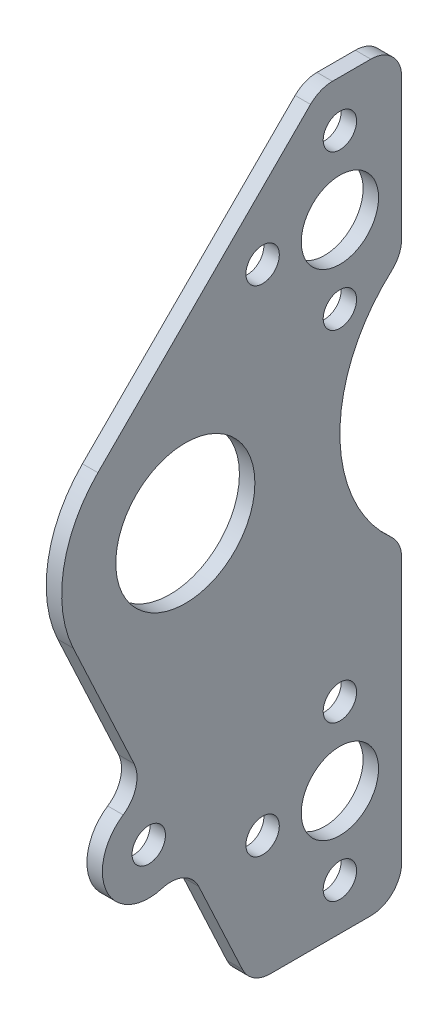
SolidWorks part; units mm, degrees
ref_plane "Front Plane" through (0, 0, 0) normal (0, 0, 1) x (1, 0, 0)
ref_plane "Top Plane" through (0, 0, 0) normal (0, 1, 0) x (1, 0, 0)
ref_plane "Right Plane" through (0, 0, 0) normal (1, 0, 0) x (0, 0, -1)
sketch "Sketch1" plane through (0, 0, 0) normal (1, 0, 0) x (0, 0, -1)
  line L0 (0, 55) -> (0, -55) construction
  line L1 (-19.05, 0) -> (-26.5619, -53.4497) construction
  line L2 (12.7, 38.1) -> (12.7, 53.975) construction
  line L3 (12.7, 38.1) -> (-3.175, 38.1) construction
  line L4 (12.7, -63.5) -> (-3.175, -63.5) construction
  line L5 (25.4, 57.15) -> (25.4, 28.3981)
  line L6 (19.05, -88.9) -> (-1.5757, -88.9)
  line L8 (11.1592, 63.5) -> (19.05, 63.5)
  line L9 (55, 0) -> (-55, 0) construction
  line L10 (-37.0105, 17.9605) -> (6.6691, 61.6401)
  line L11 (-42.0702, -10.7345) -> (-29.5744, -37.5319)
  line L12 (-16.3045, -65.9893) -> (-7.3307, -85.2336)
  line L13 (25.4, -28.3981) -> (25.4, -82.55)
  circle A0 centre (-19.05, 0) radius 14.2875
  circle A1 centre (12.7, 38.1) radius 7.9375
  circle A2 centre (12.7, -63.5) radius 7.9375
  circle A3 centre (-26.5619, -53.4497) radius 3.429
  circle A4 centre (12.7, 38.1) radius 15.875 construction
  circle A6 centre (12.7, 53.975) radius 3.429
  circle A8 centre (12.7, -63.5) radius 15.875 construction
  circle A9 centre (-3.175, -63.5) radius 3.429
  circle A10 centre (12.7, -47.625) radius 3.429
  circle A12 centre (12.7, -79.375) radius 3.429
  arc A14 (25.4, -82.55) -> (19.05, -88.9) centre (19.05, -82.55) cw
  arc A15 (25.4, 57.15) -> (19.05, 63.5) centre (19.05, 57.15) ccw
  circle A17 centre (-3.175, 38.1) radius 3.429
  circle A18 centre (12.7, 22.225) radius 3.429
  circle A19 centre (28.575, -63.5) radius 3.429 [skipped]
  arc A20 (-37.0105, 17.9605) -> (-42.0702, -10.7345) centre (-19.05, 0) ccw
  arc A21 (-31.8224, -45.5092) -> (-23.8605, -62.5836) centre (-26.5619, -53.4497) ccw
  arc A22 (-16.3045, -65.9893) -> (-23.8605, -62.5836) centre (-22.0596, -68.6729) ccw
  arc A23 (-31.8224, -45.5092) -> (-29.5744, -37.5319) centre (-35.3295, -40.2155) ccw
  arc A24 (-7.3307, -85.2336) -> (-1.5757, -88.9) centre (-1.5757, -82.55) ccw
  arc A25 (6.6691, 61.6401) -> (11.1592, 63.5) centre (11.1592, 57.15) cw
  arc A26 (23.2833, 23.6651) -> (23.2833, -23.6651) centre (44.45, 0) ccw
  arc A27 (25.4, -28.3981) -> (23.2833, -23.6651) centre (19.05, -28.3981) ccw
  arc A28 (25.4, 28.3981) -> (23.2833, 23.6651) centre (19.05, 28.3981) cw
  point P50 (0, 0)
  dimension "D1" = 15.875
  dimension "D2" = 28.575
  dimension "D6" = 6.858
  dimension "D8" = 31.75
  dimension "D12" = 4
  dimension "D18" = 19.05
  dimension "D19" = 6.858
  dimension "D15" = 45
  dimension "D23" = 50.8
  dimension "D25" = 6.35
  dimension "D26" = 63.5
  dimension "D27" = 63.5
  dimension "D28" = 6.35
  dimension "D3" = 38.1
  dimension "D4" = 63.5
  dimension "D5" = 53.975
  dimension "D7" = 8
  dimension "D10" = 90
  dimension "D11" = 15.875
  dimension "D13" = 15.875
  dimension "D14" = 25.4
  dimension "D16" = 63.5
  dimension "D17" = 88.9
  dimension "D20" = 12.7
  dimension "D21" = 12.7
  dimension "D22" = 19.05
  dimension "D24" = 65
  dimension "D9" = 3
extrude "Boss-Extrude1" add sketch "Sketch1" along normal blind 3.175
